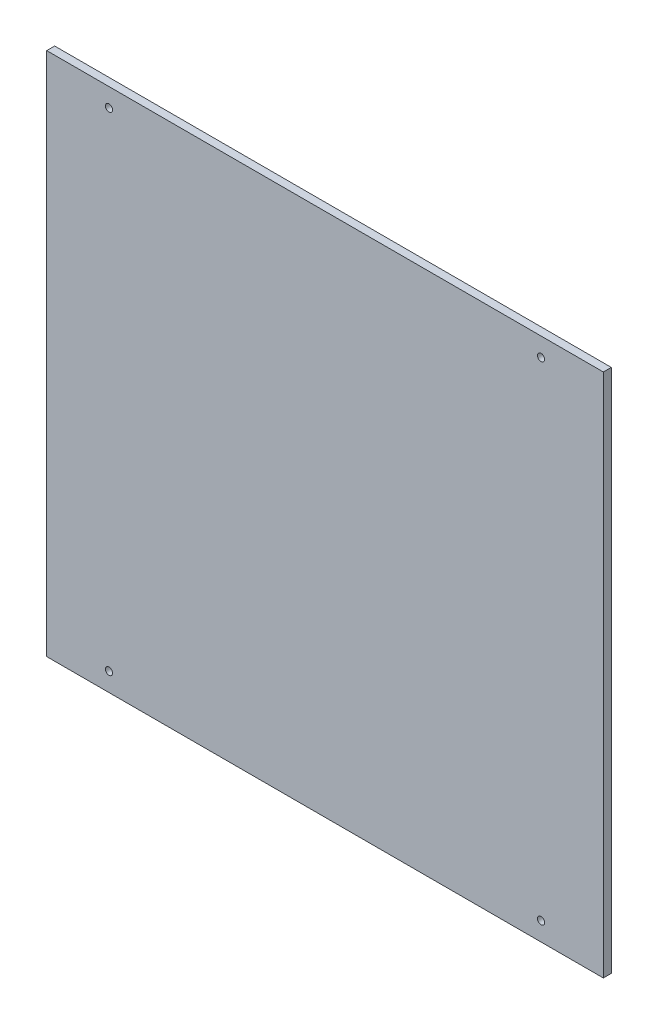
SolidWorks part; units mm, degrees
material "ABS"
ref_plane "Plan de face" through (0, 0, 0) normal (0, 0, 1) x (1, 0, 0)
ref_plane "Plan de dessus" through (0, 0, 0) normal (0, 1, 0) x (1, 0, 0)
ref_plane "Plan de droite" through (0, 0, 0) normal (1, 0, 0) x (0, 0, -1)
sketch "Esquisse1" plane through (0, 0, 0) normal (0, 0, 1) x (1, 0, 0)
  line L0 (-78, -25.5) -> (-9, -25.5) construction
  line L5 (-81.5, -92) -> (81.5, -92) construction
  line L6 (-81.5, -92) -> (-81.5, 92) construction
  line L7 (-81.5, 92) -> (81.5, 92) construction
  line L8 (81.5, -92) -> (81.5, 92) construction
  line L9 (-81.5, -92) -> (81.5, 92) construction
  line L10 (-81.5, 92) -> (81.5, -92) construction
  line L11 (-89, 79) -> (89, 79) construction
  line L12 (-89, 79) -> (-89, -79) construction
  line L13 (-89, -79) -> (89, -79) construction
  line L14 (89, 79) -> (89, -79) construction
  line L15 (-89, 79) -> (89, -79) construction
  line L16 (-89, -79) -> (89, 79) construction
  line L17 (-78, 76.5) -> (-9, 76.5) construction
  line L18 (-78, 76.5) -> (-78, 25.5) construction
  line L19 (-78, 25.5) -> (-9, 25.5) construction
  line L20 (-9, 76.5) -> (-9, 25.5) construction
  line L21 (-78, 76.5) -> (-9, 25.5) construction
  line L22 (-78, 25.5) -> (-9, 76.5) construction
  line L23 (-78, -25.5) -> (-78, -76.5) construction
  line L24 (-78, -76.5) -> (-9, -76.5) construction
  line L25 (-9, -25.5) -> (-9, -76.5) construction
  line L26 (-78, -25.5) -> (-9, -76.5) construction
  line L27 (-78, -76.5) -> (-9, -25.5) construction
  line L28 (-16.2686, 0) -> (12.6201, 0) construction
  line L29 (25, 38) -> (101, 38) construction
  line L30 (25, 38) -> (25, -38) construction
  line L31 (25, -38) -> (101, -38) construction
  line L32 (101, 38) -> (101, -38) construction
  line L33 (25, 38) -> (101, -38) construction
  line L34 (25, -38) -> (101, 38) construction
  line L36 (-105, 99) -> (105, 99)
  line L37 (-105, 99) -> (-105, -99)
  line L38 (-105, -99) -> (105, -99)
  line L39 (105, 99) -> (105, -99)
  line L40 (-105, 99) -> (105, -99) construction
  line L41 (-105, -99) -> (105, 99) construction
  point P0 (0, 0)
  point P7 (0, 0)
  point P12 (-43.5, 51)
  point P17 (-43.5, -51)
  point P22 (63, 0)
  point P29 (0, 0)
  dimension "D1" = 163
  dimension "D2" = 184
  dimension "D3" = 178
  dimension "D4" = 158
  dimension "D5" = 69
  dimension "D6" = 51
  dimension "D9" = 51
  dimension "D10" = 76
  dimension "D11" = 76
  dimension "D12" = 11
  dimension "D13" = 56.5
  dimension "D14" = 210
  dimension "D15" = 198
extrude "Boss.-Extru.1" add sketch "Esquisse1" along normal blind 3
hole_wizard "Dégagement M2.51" positions "Esquisse2" profile "Esquisse3" hole size "M2.5" standard "ISO" end condition up to next
sketch "Esquisse2" plane through (0, 0, 3) normal (0, 0, 1) x (1, 0, 0)
  point P0 (-81.5, -92)
  point P30 (-81.5, 92)
  point P48 (81.5, 92)
  point P51 (81.5, -92)
sketch "Esquisse3" plane through (-81.5, -92, 3) normal (1, 0, 0) x (0, -1, 0)
  line L0 (0, 0) -> (0, 3)
  line L1 (0, 3) -> (1.35, 3)
  line L2 (1.35, 3) -> (1.35, 0)
  line L5 (1.35, 0) -> (0, 0)
  line L11 (0, -6.35) -> (0, 107.95) construction
  dimension "Diamètre du perçage jusqu'au prochain" = 2.7
  dimension "Profondeur du perçage jusqu'au prochain" = 3
